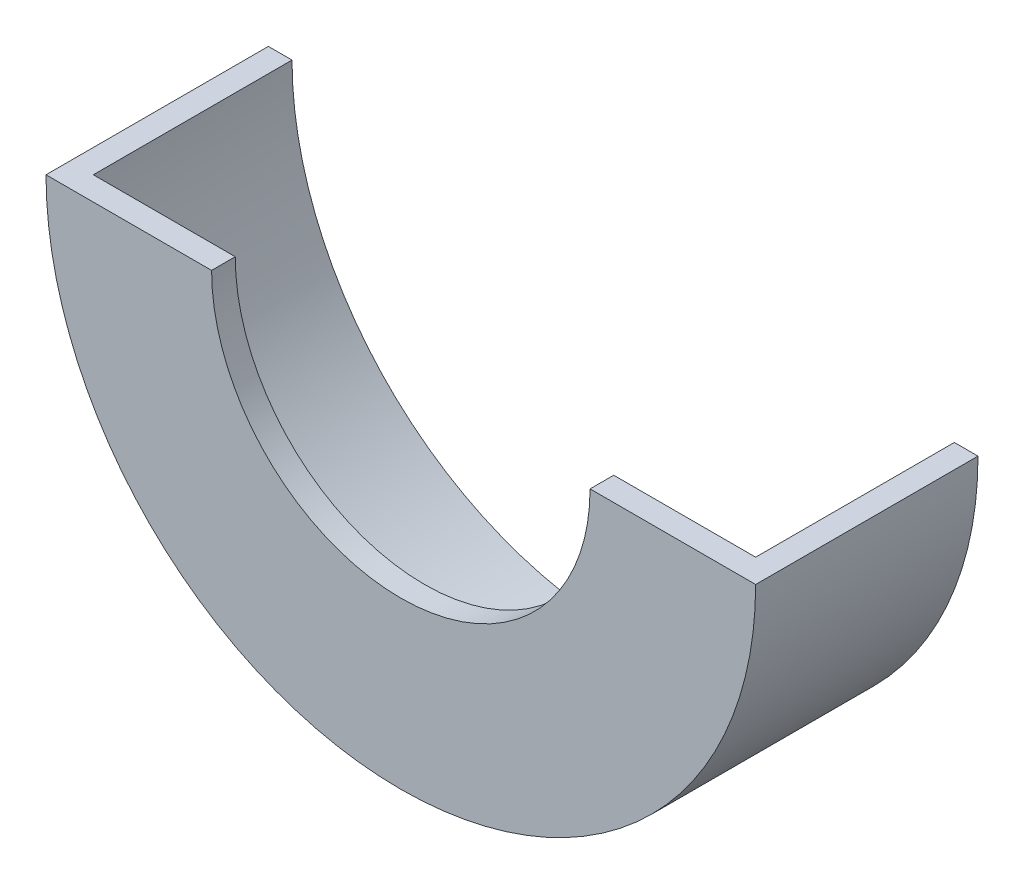
SolidWorks part; units mm, degrees
ref_plane "Front Plane" through (0, 0, 0) normal (0, 0, 1) x (1, 0, 0)
ref_plane "Top Plane" through (0, 0, 0) normal (0, 1, 0) x (1, 0, 0)
ref_plane "Right Plane" through (0, 0, 0) normal (1, 0, 0) x (0, 0, -1)
sketch "Sketch1" plane through (0, 0, 0) normal (0, 0, 1) x (1, 0, 0)
  line L0 (-75, 0) -> (75, 0)
  circle A0 centre (0, 0) radius 75
  circle A1 centre (0, 0) radius 70
  point P7 (0, 0)
extrude "Boss-Extrude1" add sketch "Sketch1" along normal blind 42 contours A1 L0 A0
sketch "Sketch2" plane through (0, 0, 42) normal (0, 0, 1) x (1, 0, 0)
  line L0 (-80, 0) -> (80, 0)
  circle A0 centre (0, 0) radius 80
  circle A1 centre (0, 0) radius 40
  point P7 (0, 0)
  arc M1 (70, 0) -> (-70, 0) centre (0, 0) cw
  line M2 (-70, 0) -> (-75, 0)
  arc M3 (-75, 0) -> (75, 0) centre (0, 0) ccw
  line M4 (75, 0) -> (70, 0)
extrude "Boss-Extrude2" add sketch "Sketch2" along normal blind 5 contours M4 M1 M2 M3 | A1 L0 M1
